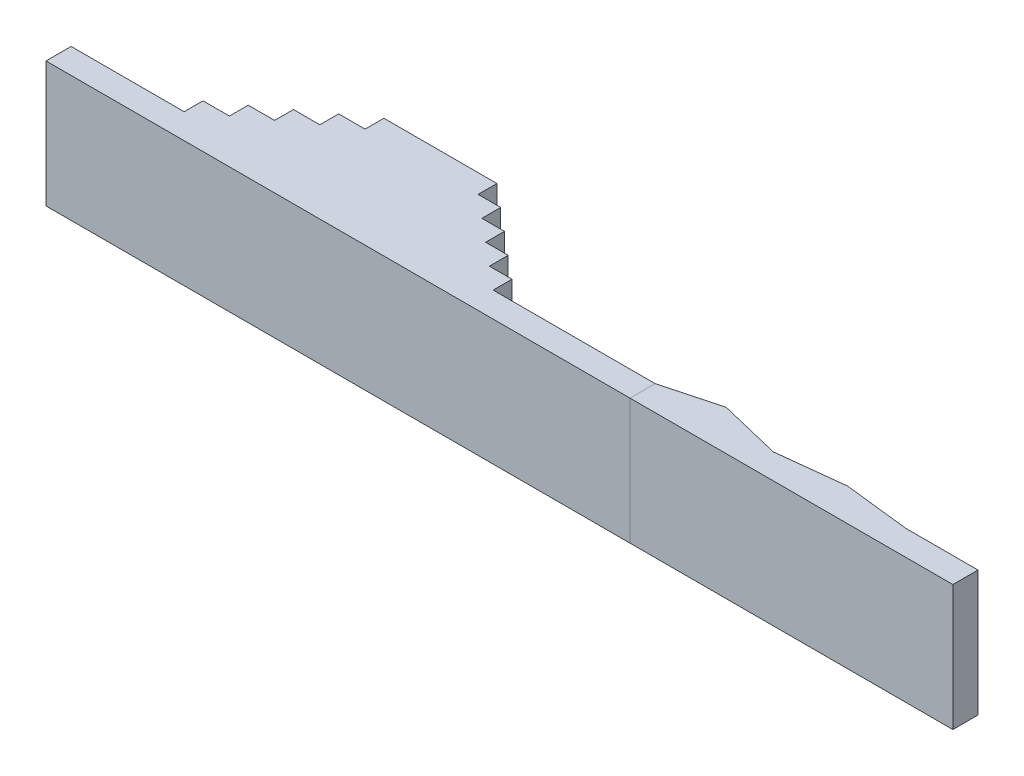
SolidWorks part; units mm, degrees
material "Cedar"
ref_plane "Front Plane" through (0, 0, 0) normal (0, 0, 1) x (1, 0, 0)
ref_plane "Top Plane" through (0, 0, 0) normal (0, 1, 0) x (1, 0, 0)
ref_plane "Right Plane" through (0, 0, 0) normal (1, 0, 0) x (0, 0, -1)
sketch "Sketch1" plane through (0, 0, 0) normal (0, 1, 0) x (1, 0, 0)
  line L0 (0, 0) -> (0, 150)
  line L1 (0, 0) -> (-900, 0)
  line L2 (0, 150) -> (210, 150)
  line L3 (210, 150) -> (210, 300)
  line L4 (210, 300) -> (420, 300)
  line L5 (420, 300) -> (420, 450)
  line L6 (420, 450) -> (630, 450)
  line L7 (630, 450) -> (630, 600)
  line L8 (630, 600) -> (840, 600)
  line L9 (840, 600) -> (840, 750)
  line L10 (840, 750) -> (1740, 750)
  line L11 (1740, 750) -> (1740, 600)
  line L12 (1740, 600) -> (1920, 600)
  line L13 (1920, 600) -> (1920, 450)
  line L14 (1920, 450) -> (2100, 450)
  line L15 (2100, 450) -> (2100, 300)
  line L16 (2100, 300) -> (2280, 300)
  line L17 (2280, 300) -> (2280, 150)
  line L18 (2280, 150) -> (2460, 150)
  line L19 (2460, 150) -> (2460, 0)
  line L20 (2460, 0) -> (3750, 0)
  line L21 (-900, 0) -> (-900, -200)
  line L22 (-900, -200) -> (3750, -200)
  line L23 (3750, 0) -> (3750, -200)
extrude "Boss-Extrude1" add sketch "Sketch1" along normal blind 1000
sketch "Sketch2" plane through (0, 1000, 0) normal (0, 1, 0) x (1, 0, 0)
  line L0 (3750, -200) -> (6320, -200)
  line L1 (6320, -200) -> (6320, 0)
  line L2 (3750, 0) -> (4196.0433, 119.5525)
  line L3 (4196.0433, 119.5525) -> (4688.8856, 0)
  line L4 (4688.8856, 0) -> (5223.8512, 59.7763)
  line L5 (5223.8512, 59.7763) -> (5746.1798, 0)
  line L6 (5746.1798, 0) -> (6320, 0)
  line L32 (0, 0) -> (-900, 0)
  line L33 (-900, 0) -> (-900, -200)
  line L34 (-900, -200) -> (3750, -200)
  line L35 (3750, -200) -> (3750, 0)
  line L36 (3750, 0) -> (2460, 0)
  line L37 (2460, 0) -> (2460, 150)
  line L38 (2460, 150) -> (2280, 150)
  line L39 (2280, 150) -> (2280, 300)
  line L40 (2280, 300) -> (2100, 300)
  line L41 (2100, 300) -> (2100, 450)
  line L42 (2100, 450) -> (1920, 450)
  line L43 (1920, 450) -> (1920, 600)
  line L44 (1920, 600) -> (1740, 600)
  line L45 (1740, 600) -> (1740, 750)
  line L46 (1740, 750) -> (840, 750)
  line L47 (840, 750) -> (840, 600)
  line L48 (840, 600) -> (630, 600)
  line L49 (630, 600) -> (630, 450)
  line L50 (630, 450) -> (420, 450)
  line L51 (420, 450) -> (420, 300)
  line L52 (420, 300) -> (210, 300)
  line L53 (210, 300) -> (210, 150)
  line L54 (210, 150) -> (0, 150)
  line L55 (0, 150) -> (0, 0)
  line L59 (3750, -200) -> (3750, 0)
  dimension "D1" = 0
extrude "Boss-Extrude3" add sketch "Sketch2" against normal blind 1000 separate body
